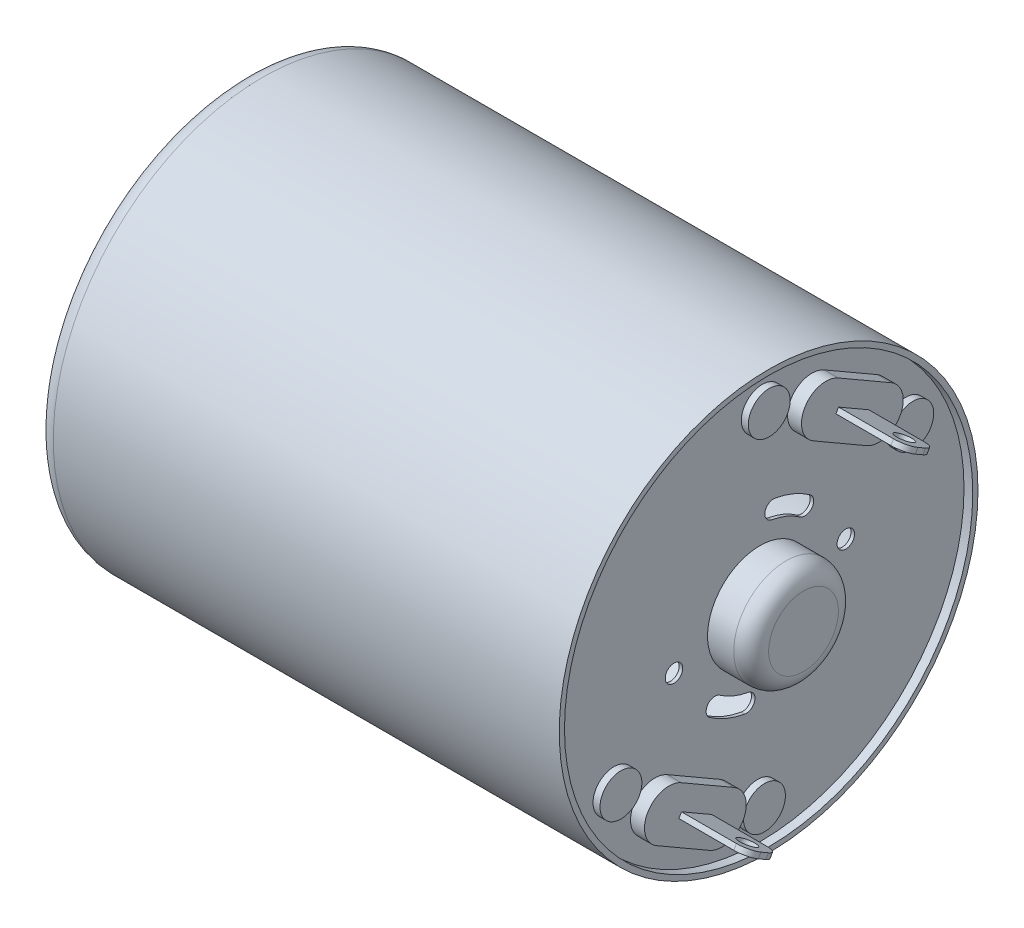
SolidWorks part; units mm, degrees
ref_plane "Front Plane" through (0, 0, 0) normal (0, 0, 1) x (1, 0, 0)
ref_plane "Top Plane" through (0, 0, 0) normal (0, 1, 0) x (1, 0, 0)
ref_plane "Right Plane" through (0, 0, 0) normal (1, 0, 0) x (0, 0, -1)
sketch "Sketch1" plane through (0, 0, 0) normal (1, 0, 0) x (0, 0, -1)
  circle A0 centre (0, 0) radius 12
  circle A1 centre (0, 0) radius 11.7
  dimension "D1" = 0.3
  dimension "D2" = 24
extrude "Boss-Extrude1" add sketch "Sketch1" against normal blind 30
ref_plane "Plane1" through (-0.5, 0, 0) normal (1, 0, 0) x (0, 0, -1)
sketch "Sketch2" plane through (-0.5, 0, 0) normal (1, 0, 0) x (0, 0, -1)
  circle A0 centre (0, 0) radius 11.7
  circle A1 centre (0, 0) radius 11.7 construction
extrude "Boss-Extrude2" add sketch "Sketch2" against normal blind 0.2
sketch "Sketch3" plane through (-0.5, 0, 0) normal (1, 0, 0) x (0, 0, -1)
  circle A0 centre (0, 0) radius 3
  dimension "D1" = 6
extrude "Boss-Extrude3" add sketch "Sketch3" along normal blind 2.5
fillet "Fillet1" radius 1 1 edges at (2, 0, -3)
sketch "Sketch4" plane through (-0.5, 0, 0) normal (1, 0, 0) x (0, 0, -1)
  line L0 (0, 0) -> (0.7814, 4.4316) construction
  line L1 (0, 0) -> (2.5811, 3.6862) construction
  line L2 (0, 0) -> (0, 12) construction
  arc A0 (2.5811, 3.6862) -> (0.7814, 4.4316) centre (0, 0) ccw construction
  arc A1 (2.8679, 4.0958) -> (0.8682, 4.924) centre (0, 0) ccw
  arc A2 (2.2943, 3.2766) -> (0.6946, 3.9392) centre (0, 0) ccw
  arc A3 (2.2943, 3.2766) -> (2.8679, 4.0958) centre (2.5811, 3.6862) ccw
  arc A4 (0.8682, 4.924) -> (0.6946, 3.9392) centre (0.7814, 4.4316) ccw
  circle A5 centre (0, 0) radius 12 construction
  point P4 (1.7221, 4.1575)
  dimension "D1" = 4.5
  dimension "D4" = 0.5
  dimension "D2" = 10
  dimension "D3" = 25
extrude "Cut-Extrude1" cut sketch "Sketch4" against normal through all
pattern_circular "CirPattern1" count 2 over 360 about axis through (0, 0, 0) along (1, 0, 0) of "Cut-Extrude1"
sketch "Sketch5" plane through (-0.5, 0, 0) normal (1, 0, 0) x (0, 0, -1)
  line L0 (0, 0) -> (11.7, 0) construction
  line L1 (0, 0) -> (4.924, 0.8682) construction
  circle A0 centre (4.924, 0.8682) radius 0.5
  circle A1 centre (0, 0) radius 11.7 construction
  dimension "D1" = 1
  dimension "D2" = 10
  dimension "D3" = 5
extrude "Cut-Extrude2" cut sketch "Sketch5" against normal through all
pattern_circular "CirPattern2" count 2 over 360 about axis through (0, 0, 0) along (1, 0, 0) of "Cut-Extrude2"
sketch "Sketch7" plane through (-30, 0, 0) normal (-1, 0, 0) x (0, 0, 1)
  circle A0 centre (0, 0) radius 11.7
  circle A1 centre (0, 0) radius 11.7 construction
extrude "Boss-Extrude4" add sketch "Sketch7" against normal blind 0.3
sketch "Sketch9" plane through (-30, 0, 0) normal (-1, 0, 0) x (0, 0, 1)
  circle A0 centre (0, 0) radius 3
  dimension "D1" = 6
extrude "Cut-Extrude3" cut sketch "Sketch9" against normal up to next
sketch "Sketch6" plane through (-0.5, 0, 0) normal (1, 0, 0) x (0, 0, -1)
  line L0 (2.9845, 8.6692) -> (6.0155, 6.9192) construction
  line L1 (3.6845, 9.8817) -> (6.7155, 8.1317)
  line L2 (2.2845, 7.4568) -> (5.3155, 5.7068)
  line L3 (0, 0) -> (4.5, 7.7942) construction
  line L4 (0, 0) -> (12, 0) construction
  arc A0 (3.6845, 9.8817) -> (2.2845, 7.4568) centre (2.9845, 8.6692) ccw
  arc A1 (5.3155, 5.7068) -> (6.7155, 8.1317) centre (6.0155, 6.9192) ccw
  circle A2 centre (0, 0) radius 12 construction
  point P2 (4.5, 7.7942)
  dimension "D1" = 1.4
  dimension "D2" = 3.5
  dimension "D3" = 60
  dimension "D4" = 9
extrude "Boss-Extrude5" add sketch "Sketch6" along normal blind 0.8
sketch "Sketch10" plane through (-0.5, 0, 0) normal (1, 0, 0) x (0, 0, -1)
  line L0 (0.1364, 9.7362) -> (8.3636, 4.9862) construction
  line L1 (2.2845, 7.4568) -> (5.3155, 5.7068) construction
  line L2 (5.2, 9.0067) -> (4.25, 7.3612) construction
  line L3 (6.7155, 8.1317) -> (3.6845, 9.8817) construction
  circle A0 centre (0.1364, 9.7362) radius 1.2
  circle A1 centre (8.3636, 4.9862) radius 1.2
  arc A2 (3.6845, 9.8817) -> (2.2845, 7.4568) centre (2.9845, 8.6692) ccw construction
  point P6 (1.772, 9.3692)
  dimension "D3" = 2.4
  dimension "D1" = 0.5
  dimension "D2" = 9.5
extrude "Boss-Extrude6" add sketch "Sketch10" along normal blind 0.4
sketch "Sketch11" plane through (0.3, 0, 0) normal (1, 0, 0) x (0, 0, -1)
  line L0 (3.8, 6.5818) -> (5.2, 9.0067) construction
  line L1 (3.709, 8.4241) -> (5.441, 7.4241)
  line L2 (3.709, 8.4241) -> (3.559, 8.1643)
  line L3 (3.559, 8.1643) -> (5.291, 7.1643)
  line L4 (5.441, 7.4241) -> (5.291, 7.1643)
  line L6 (3.709, 8.4241) -> (5.291, 7.1643) construction
  line L7 (3.559, 8.1643) -> (5.441, 7.4241) construction
  line L8 (2.2845, 7.4568) -> (5.3155, 5.7068) construction
  line L9 (6.7155, 8.1317) -> (3.6845, 9.8817) construction
  point P0 (4.5, 7.7942)
  dimension "D1" = 0.3
  dimension "D2" = 2
extrude "Boss-Extrude7" add sketch "Sketch11" along normal blind 3.9
sketch "Sketch12" plane through (0, 7.6643, -4.425) normal (0, -0.866, 0.5) x (-1, 0, 0)
  line L0 (-4.2, 0) -> (-3.2, 0) construction
  line L1 (-4.2, -1) -> (-4.2, 1) construction
  circle A0 centre (-3.2, 0) radius 0.5
  dimension "D2" = 1
  dimension "D1" = 1
extrude "Cut-Extrude4" cut sketch "Sketch12" against normal through all
fillet "Fillet3" radius 0.75 2 edges at (4.2, 8.2942, -3.634) (4.2, 7.2942, -5.366)
pattern_circular "CirPattern3" count 2 over 360 about axis through (0, 0, 0) along (1, 0, 0) of "Boss-Extrude5", "Fillet3", "Boss-Extrude7", "Cut-Extrude4"
sketch "Sketch13" plane through (-30, 0, 0) normal (-1, 0, 0) x (0, 0, 1)
  circle A0 centre (0, 0) radius 3
  circle A1 centre (0, 0) radius 3 construction
extrude "Boss-Extrude8" add sketch "Sketch13" against normal blind 0.3 separate body
sketch "Sketch14" plane through (-30, 0, 0) normal (-1, 0, 0) x (0, 0, 1)
  circle A0 centre (0, 0) radius 1
  dimension "D1" = 2
extrude "Cut-Extrude5" cut sketch "Sketch14" against normal up to next (0.3 mm away)
fillet "Fillet2" radius 1 1 edges at (-30, 0, -12)
pattern_circular "CirPattern4" count 2 over 360 about axis through (0, 0, 0) along (1, 0, 0) of "Boss-Extrude6"
